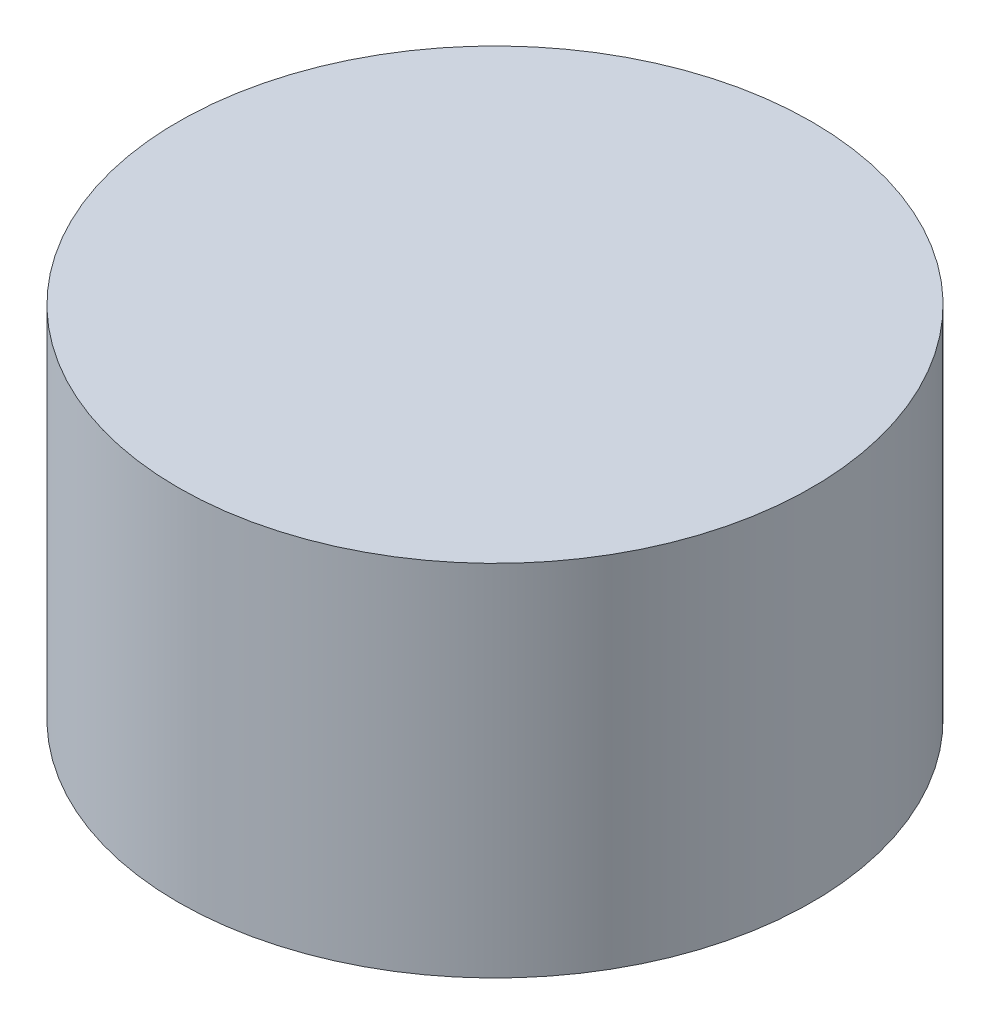
SolidWorks part; units mm, degrees
ref_plane "Front Plane" through (0, 0, 0) normal (0, 0, 1) x (1, 0, 0)
ref_plane "Top Plane" through (0, 0, 0) normal (0, 1, 0) x (1, 0, 0)
ref_plane "Right Plane" through (0, 0, 0) normal (1, 0, 0) x (0, 0, -1)
sketch "Sketch2" plane through (0, 0, 0) normal (0, 1, 0) x (1, 0, 0)
  circle A0 centre (0, 0) radius 15
  dimension "D1" = 30
extrude "Boss-Extrude1" add sketch "Sketch2" along normal blind 17
